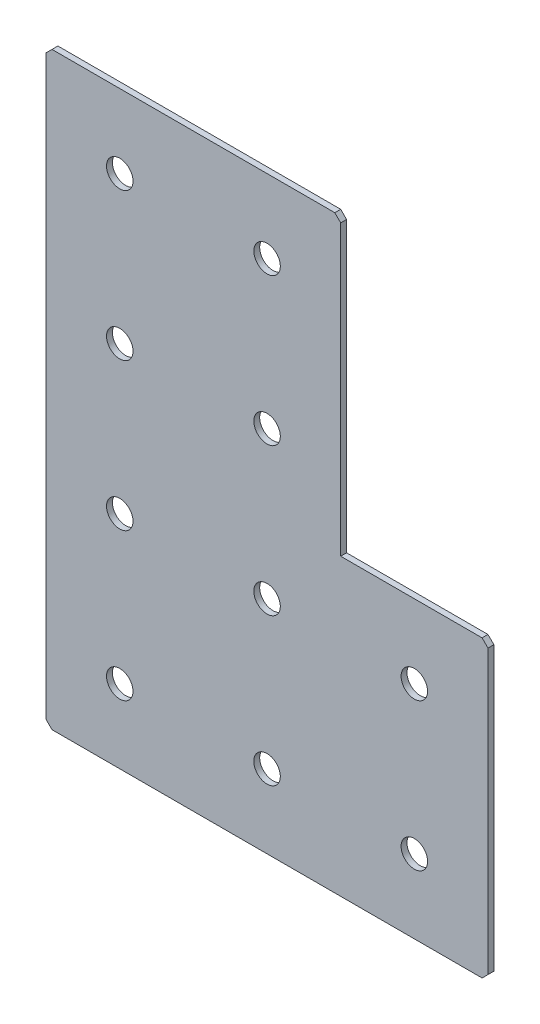
SolidWorks part; units mm, degrees
material "Простая углеродистая сталь"
ref_plane "Спереди(Плоскость XY)" through (0, 0, 0) normal (0, 0, 1) x (1, 0, 0)
ref_plane "Сверху(Плоскость XZ)" through (0, 0, 0) normal (0, 1, 0) x (1, 0, 0)
ref_plane "Справа(Плоскость ZY)" through (0, 0, 0) normal (1, 0, 0) x (0, 0, -1)
sketch "Эскиз1" plane through (0, 0, 0) normal (0, 0, -1) x (1, 0, 0)
  line L0 (0, 0) -> (0, 200)
  line L1 (0, 200) -> (150, 200)
  line L2 (150, 200) -> (150, 100)
  line L3 (150, 100) -> (100, 100)
  line L4 (100, 100) -> (100, 0)
  line L5 (100, 0) -> (0, 0)
  line L6 (150, 100) -> (100, 0) construction
  dimension "D1" = 200
  dimension "D3" = 100
  dimension "D4" = 150
extrude "Бобышка-Вытянуть1" add sketch "Эскиз1" along normal blind 2
hole_wizard "Отверстие с зазором M81" positions "Эскиз2" profile "Эскиз3" hole size "M8" standard "DIN" end condition through all
sketch "Эскиз2" plane through (0, 0, -2) normal (0, 0, -1) x (1, 0, 0)
  line L5 (25, 175) -> (75, 175) construction
  line L6 (75, 175) -> (125, 175) construction
  line L8 (25, 175) -> (25, 125) construction
  line L9 (25, 125) -> (25, 75) construction
  line L10 (25, 75) -> (25, 25) construction
  line L12 (0, 200) -> (0, 0) construction
  line L13 (150, 200) -> (0, 200) construction
  point P0 (25, 175)
  point P2 (25, 125)
  point P4 (25, 75)
  point P6 (25, 25)
  point P27 (75, 175)
  point P29 (75, 125)
  point P35 (75, 75)
  point P37 (75, 25)
  point P39 (125, 175)
  point P41 (125, 125)
  point P64 (0, 0)
  point P65 (0, 0)
  point P66 (0, 0)
  point P67 (0, 0)
  point P73 (0, 0)
  dimension "D1" = 50
  dimension "D2" = 25
  dimension "D3" = 25
sketch "Эскиз3" plane through (25, -175, -2) normal (1, 0, 0) x (0, 1, 0)
  line L0 (0, 0) -> (0, 2)
  line L1 (0, 2) -> (4.5, 2)
  line L2 (4.5, 2) -> (4.5, 0)
  line L5 (4.5, 0) -> (0, 0)
  line L11 (0, -6.35) -> (0, 107.95) construction
  dimension "Диаметр сквозного отверстия" = 9
  dimension "Глубина сквозного отверстия" = 2
chamfer "Фаска1" distance 2 angle 45 5 edges at (0, 0, -1) (100, 0, -1) (150, -100, -1) (150, -200, -1) (0, -200, -1)
